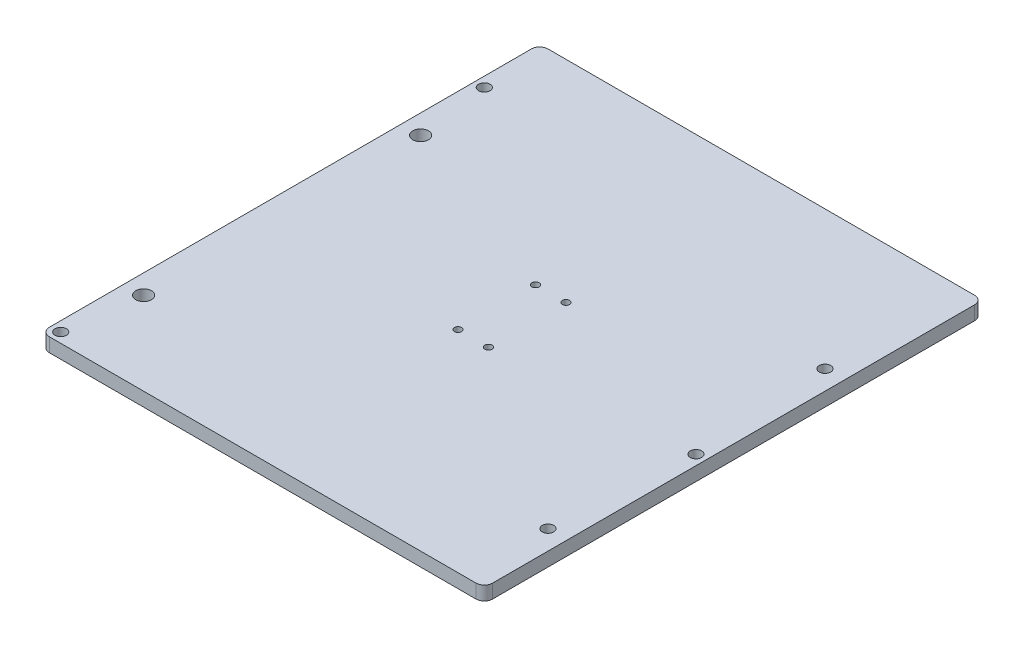
SolidWorks part; units mm, degrees
material "Pine"
ref_plane "Front Plane" through (0, 0, 0) normal (0, 0, 1) x (1, 0, 0)
ref_plane "Top Plane" through (0, 0, 0) normal (0, 1, 0) x (1, 0, 0)
ref_plane "Right Plane" through (0, 0, 0) normal (1, 0, 0) x (0, 0, -1)
sketch "Sketch1" plane through (0, 0, 0) normal (0, 1, 0) x (1, 0, 0)
  line L1 (0, 0) -> (203.2, 0) construction
  line L2 (0, 0) -> (0, 203.2)
  line L3 (0, 203.2) -> (203.2, 203.2)
  line L4 (203.2, 0) -> (203.2, 203.2)
  line L5 (0, 0) -> (203.2, 0) construction
  line L6 (0, 0) -> (0, -25.4)
  line L7 (0, -25.4) -> (203.2, -25.4)
  line L8 (203.2, 0) -> (203.2, -25.4)
  dimension "D1" = 203.2
  dimension "D2" = 203.2
  dimension "D3" = 25.4
extrude "Boss-Extrude1" add sketch "Sketch1" along normal blind 6.35
sketch "Sketch2" plane through (0, 6.35, 0) normal (0, 1, 0) x (1, 0, 0)
  line L0 (203.2, 203.2) -> (0, 203.2) construction
  line L2 (203.2, 203.2) -> (0, 203.2) construction
  line L3 (0, -25.4) -> (203.2, -25.4) construction
  line L4 (8.9014, 203.2) -> (8.9014, 0) construction
  line L5 (194.2986, 0) -> (194.2986, 203.2) construction
  line L7 (101.6, 203.2) -> (101.6, 0) construction
  circle A0 centre (8.9014, 12.7) radius 3.6
  circle A1 centre (8.9014, 139.7) radius 3.6
  circle A2 centre (194.2986, 12.7) radius 2.625
  circle A3 centre (194.2986, 139.7) radius 2.625
  dimension "D2" = 7.2
  dimension "D5" = 5.25
  dimension "D1" = 185.3971
  dimension "D3" = 38.1
  dimension "D4" = 63.5
extrude "wheel holes" cut sketch "Sketch2" against normal up to next
sketch "Sketch3" plane through (0, 0, 0) normal (0, -1, 0) x (1, 0, 0)
  line L0 (0, -203.2) -> (0, 25.4) construction
  line L2 (203.2, 25.4) -> (203.2, -203.2) construction
  line L3 (0, 25.4) -> (203.2, 25.4) construction
  circle A0 centre (4.5009, 20.9017) radius 2.625
  circle A1 centre (4.5009, -173.2991) radius 2.625
  circle A2 centre (198.65, -76.2) radius 2.625
  dimension "D1" = 5.25
  dimension "D4" = 4.4983
  dimension "D2" = 194.2008
  dimension "D3" = 4.5009
  dimension "D5" = 4.55
  dimension "D6" = 101.6
extrude "build plate holes" cut sketch "Sketch3" against normal up to next
fillet "Fillet1" radius 3.81 4 edges at (203.2, 3.175, -203.2) (0, 3.175, -203.2) (203.2, 3.175, 25.4) (0, 3.175, 25.4)
sketch "Sketch4" plane through (0, 6.35, 0) normal (0, 1, 0) x (1, 0, 0)
  line L0 (101.6, 203.2) -> (101.6, -25.4) construction
  line L1 (199.39, 203.2) -> (3.81, 203.2) construction
  line L2 (3.81, -25.4) -> (199.39, -25.4) construction
  line L3 (0, 88.9) -> (203.2, 88.9) construction
  line L4 (0, 199.39) -> (0, -21.59) construction
  line L5 (203.2, -21.59) -> (203.2, 199.39) construction
  circle A0 centre (94.6, 106.68) radius 1.65
  circle A1 centre (108.6, 106.68) radius 1.65
  circle A2 centre (108.6, 71.12) radius 1.65
  circle A3 centre (94.6, 71.12) radius 1.65
  dimension "D1" = 3.3
  dimension "D2" = 14
  dimension "D3" = 7
  dimension "D4" = 17.78
extrude "belt clamp holes" cut sketch "Sketch4" against normal up to next
